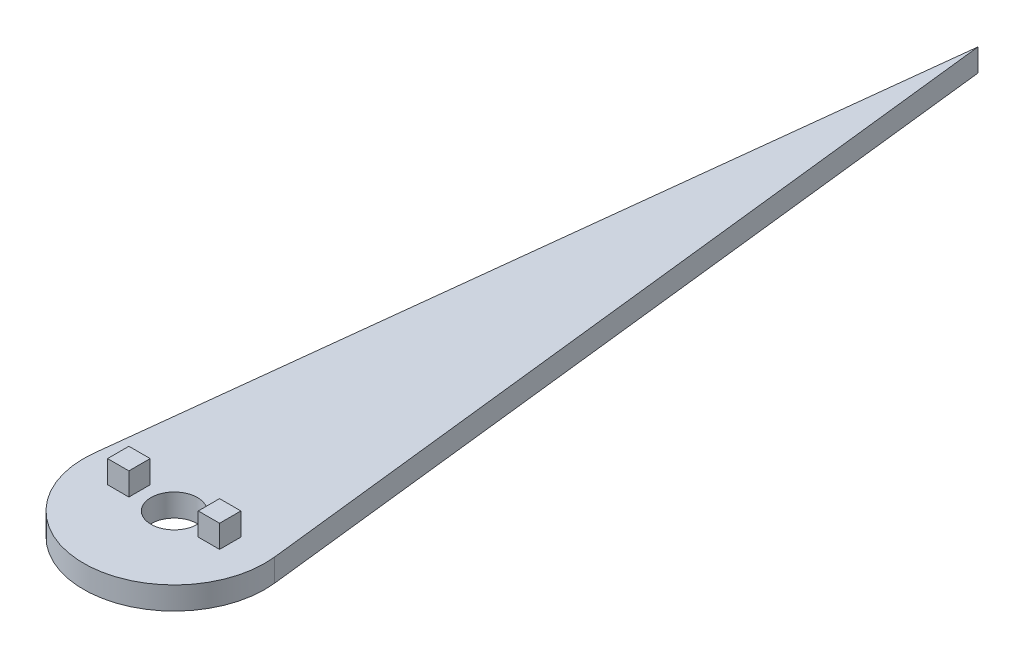
SolidWorks part; units mm, degrees
ref_plane "Front Plane" through (0, 0, 0) normal (0, 0, 1) x (1, 0, 0)
ref_plane "Top Plane" through (0, 0, 0) normal (0, 1, 0) x (1, 0, 0)
ref_plane "Right Plane" through (0, 0, 0) normal (1, 0, 0) x (0, 0, -1)
sketch "Sketch1" plane through (0, 0, 0) normal (0, 1, 0) x (1, 0, 0)
  line L0 (-19.8723, 2.2566) -> (0, 177.2566)
  line L1 (0, 177.2566) -> (19.8723, 2.2566)
  arc A0 (-19.8723, 2.2566) -> (19.8723, 2.2566) centre (0, 0) ccw
  circle A1 centre (0, 0) radius 5.125
  dimension "D1" = 10.25
  dimension "D2" = 20
  dimension "D3" = 175
extrude "Boss-Extrude1" add sketch "Sketch1" along normal blind 5
sketch "Sketch2" plane through (0, 5, 0) normal (0, 1, 0) x (1, 0, 0)
  line L1 (7.65, -2.35) -> (12.35, -2.35)
  line L2 (7.65, -2.35) -> (7.65, 2.35)
  line L3 (7.65, 2.35) -> (12.35, 2.35)
  line L4 (12.35, -2.35) -> (12.35, 2.35)
  line L5 (7.65, -2.35) -> (12.35, 2.35) construction
  line L6 (7.65, 2.35) -> (12.35, -2.35) construction
  line L7 (-12.35, -2.35) -> (-7.65, -2.35)
  line L8 (-12.35, -2.35) -> (-12.35, 2.35)
  line L9 (-12.35, 2.35) -> (-7.65, 2.35)
  line L10 (-7.65, -2.35) -> (-7.65, 2.35)
  line L11 (-12.35, -2.35) -> (-7.65, 2.35) construction
  line L12 (-12.35, 2.35) -> (-7.65, -2.35) construction
  point P0 (10, 0)
  point P5 (-10, 0)
  dimension "D1" = 4.7
  dimension "D2" = 4.7
  dimension "D3" = 10
  dimension "D4" = 10
extrude "Boss-Extrude2" add sketch "Sketch2" along normal blind 5
